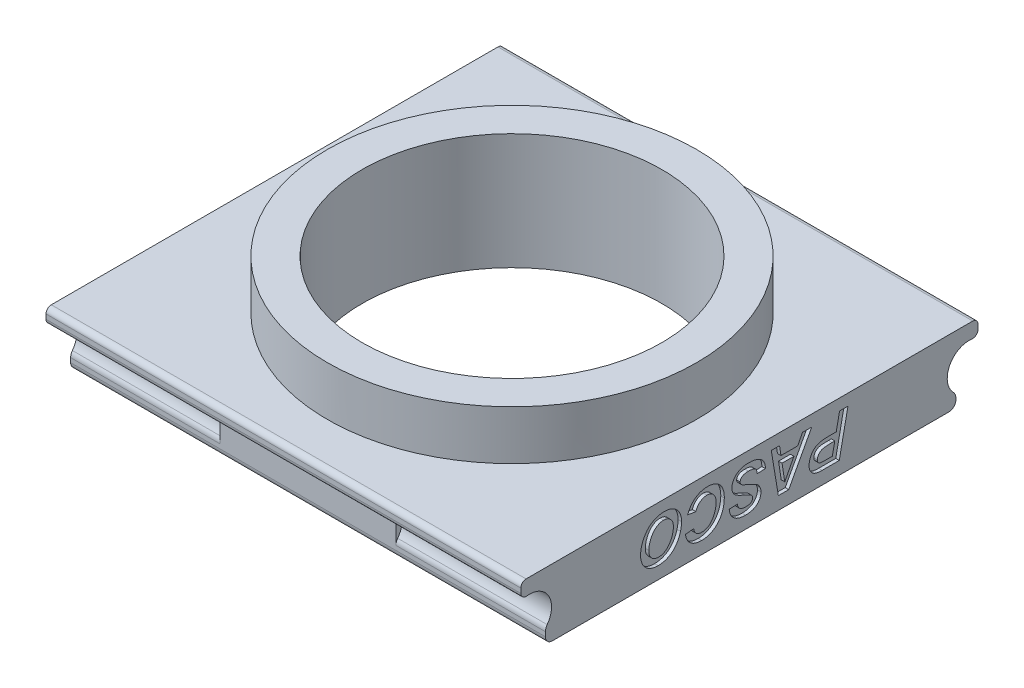
SolidWorks part; units mm, degrees
ref_plane "Front Plane" through (0, 0, 0) normal (0, 0, 1) x (1, 0, 0)
ref_plane "Top Plane" through (0, 0, 0) normal (0, 1, 0) x (1, 0, 0)
ref_plane "Right Plane" through (0, 0, 0) normal (1, 0, 0) x (0, 0, -1)
sketch "Sketch1" plane through (0, 0, 0) normal (0, 1, 0) x (1, 0, 0)
  line L1 (-34.29, 33.02) -> (34.29, 33.02)
  line L2 (-34.29, 33.02) -> (-34.29, -33.02)
  line L3 (-34.29, -33.02) -> (34.29, -33.02)
  line L4 (34.29, 33.02) -> (34.29, -33.02)
  line L5 (-34.29, 33.02) -> (34.29, -33.02) construction
  line L6 (-34.29, -33.02) -> (34.29, 33.02) construction
  point P0 (0, 0)
  dimension "D1" = 66.04
  dimension "D2" = 68.58
extrude "Boss-Extrude1 Base" add sketch "Sketch1" along normal blind 9.652 contours L2 L3 L4 L1
sketch "Sketch6" plane through (34.29, 0, 0) normal (1, 0, 0) x (0, 0, -1)
  line L0 (0, 9.9489) -> (0, 1.8604) construction
  line L1 (33.02, 0) -> (-33.02, 0) construction
  circle A0 centre (-31.75, 4.318) radius 3.175
  circle A1 centre (31.75, 4.318) radius 3.175
  dimension "D1" = 6.35
  dimension "D2" = 6.35
  dimension "D3" = 31.75
  dimension "D4" = 31.75
  dimension "D5" = 4.318
  dimension "D6" = 4.318
extrude "Cut-Extrude1" cut sketch "Sketch6" against normal through all
sketch "Sketch7" plane through (0, 9.652, 0) normal (0, 1, 0) x (1, 0, 0)
  circle A0 centre (0, 0) radius 26.67
  dimension "D1" = 53.34
extrude "Boss-Extrude3 Ring" add sketch "Sketch7" along normal blind 7.112
sketch "Sketch8" plane through (0, 16.764, 0) normal (0, 1, 0) x (1, 0, 0)
  circle A0 centre (0, 0) radius 21.6535
  dimension "D1" = 43.307
extrude "Cut-Center hole" cut sketch "Sketch8" against normal through all
sketch "Sketch9" plane through (34.29, 0, 0) normal (1, 0, 0) x (0, 0, -1)
  line L1 (-33.02, 3.376) -> (-29.464, 3.376)
  line L2 (-33.02, 3.376) -> (-33.02, -0.0182)
  line L3 (-33.02, -0.0182) -> (-29.464, -0.0182)
  line L4 (-29.464, 3.376) -> (-29.464, -0.0182)
  line L5 (33.3808, 3.2475) -> (29.8248, 3.2475)
  line L6 (33.3808, 3.2475) -> (33.3808, -0.027)
  line L7 (33.3808, -0.027) -> (29.8248, -0.027)
  line L8 (29.8248, 3.2475) -> (29.8248, -0.027)
  dimension "D1" = 3.556
extrude "Cut-Extrude3 Trim" cut sketch "Sketch9" against normal through all
sketch "Sketch10" plane through (0, 0, 0) normal (1, 0, 0) x (0, 0, -1)
  line L1 (-29.464, 2.1146) -> (-26.5329, 2.1146)
  line L2 (-29.464, 2.1146) -> (-29.464, 8.1049)
  line L3 (-29.464, 8.1049) -> (-26.5329, 8.1049)
  line L4 (-26.5329, 2.1146) -> (-26.5329, 8.1049)
  line L5 (29.8248, 1.7933) -> (26.6594, 1.7933)
  line L6 (29.8248, 1.7933) -> (29.8248, 8.0705)
  line L7 (29.8248, 8.0705) -> (26.6594, 8.0705)
  line L8 (26.6594, 1.7933) -> (26.6594, 8.0705)
extrude "Boss-Extrude4 Center stop" add sketch "Sketch10" along normal mid plane 25.4
sketch "Sketch14" plane through (0, 0, 0) normal (0, -1, 0) x (1, 0, 0)
  line L1 (21.652, 0.254) -> (28.7769, 0.254)
  line L2 (21.652, 0.254) -> (21.652, -0.3054)
  line L3 (21.652, -0.3054) -> (28.7769, -0.3054)
  line L4 (28.7769, 0.254) -> (28.7769, -0.3054)
  circle A0 centre (0, 0) radius 21.6535 construction
  dimension "D1" = 0.254
fillet "Fillet4" radius 0.762 2 edges at (0, 7.2279, 33.02) (0, 7.2279, -33.02)
fillet "Fillet5" radius 0.762 2 edges at (0, 9.652, -33.02) (0, 9.652, 33.02)
fillet "Fillet6" radius 1.27 4 edges at (23.495, 2.1146, 29.464) (-23.495, 2.1146, 29.464) (-23.495, 1.7933, -29.8248) (23.495, 1.7933, -29.8248)
fillet "Fillet7" radius 1.016 2 edges at (0, 0, -29.8248) (0, 0, 29.464)
extrude "Cut-Extrude9" cut sketch "Sketch14" against normal blind 0.254
sketch "Sketch15 PASCO" plane through (34.29, 6.3341, -8.0339) normal (1, 0, 0) x (0, 0, -1)
  line L0 (-23.75, 1.6826) -> (22.8645, 1.6826) construction
  text T0 "PASCO" font "Arial" height in points 24
extrude "Cut-Extrude10" cut sketch "Sketch15 PASCO" against normal blind 0.508
sketch "Sketch16 PASCO" plane through (-34.29, 4.7513, 6.6387) normal (-1, 0, 0) x (0, 0, 1)
  line L0 (-22.9277, 3.3172) -> (19.1961, 3.3172) construction
  text T0 "PASCO" font "Arial" height in points 24
extrude "Cut-Extrude11" cut sketch "Sketch16 PASCO" against normal blind 0.508
